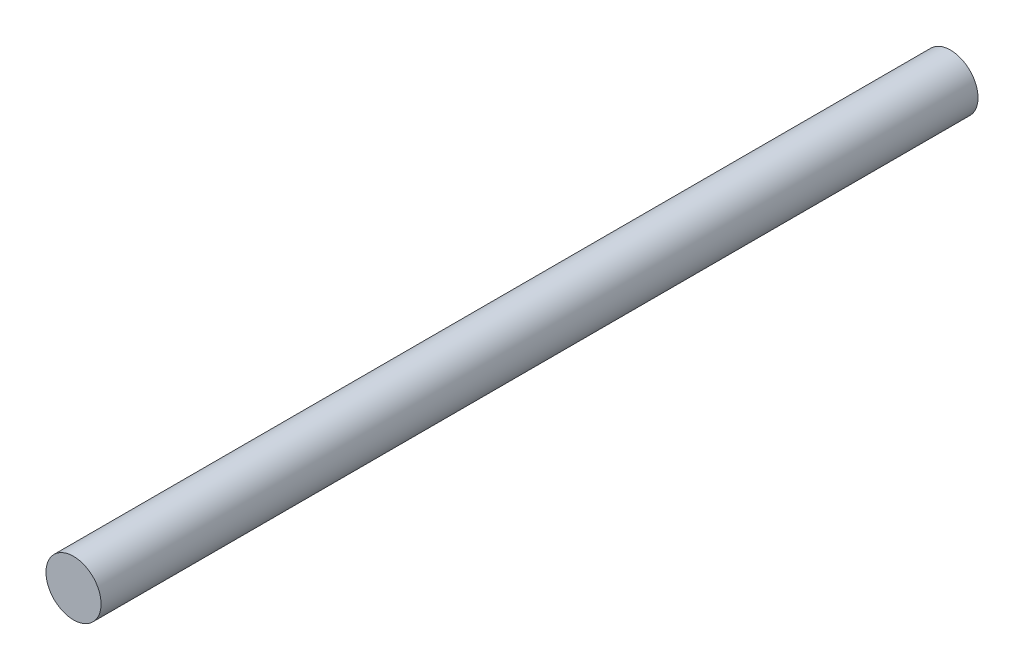
SolidWorks part; units mm, degrees
ref_plane "Plan de face" through (0, 0, 0) normal (0, 0, 1) x (1, 0, 0)
ref_plane "Plan de dessus" through (0, 0, 0) normal (0, 1, 0) x (1, 0, 0)
ref_plane "Plan de droite" through (0, 0, 0) normal (1, 0, 0) x (0, 0, -1)
sketch "Esquisse1" plane through (0, 0, 0) normal (0, 0, 1) x (1, 0, 0)
  circle A0 centre (-7.7812, 9.5608) radius 2.2
extrude "Boss.-Extru.1" add sketch "Esquisse1" along normal blind 70
